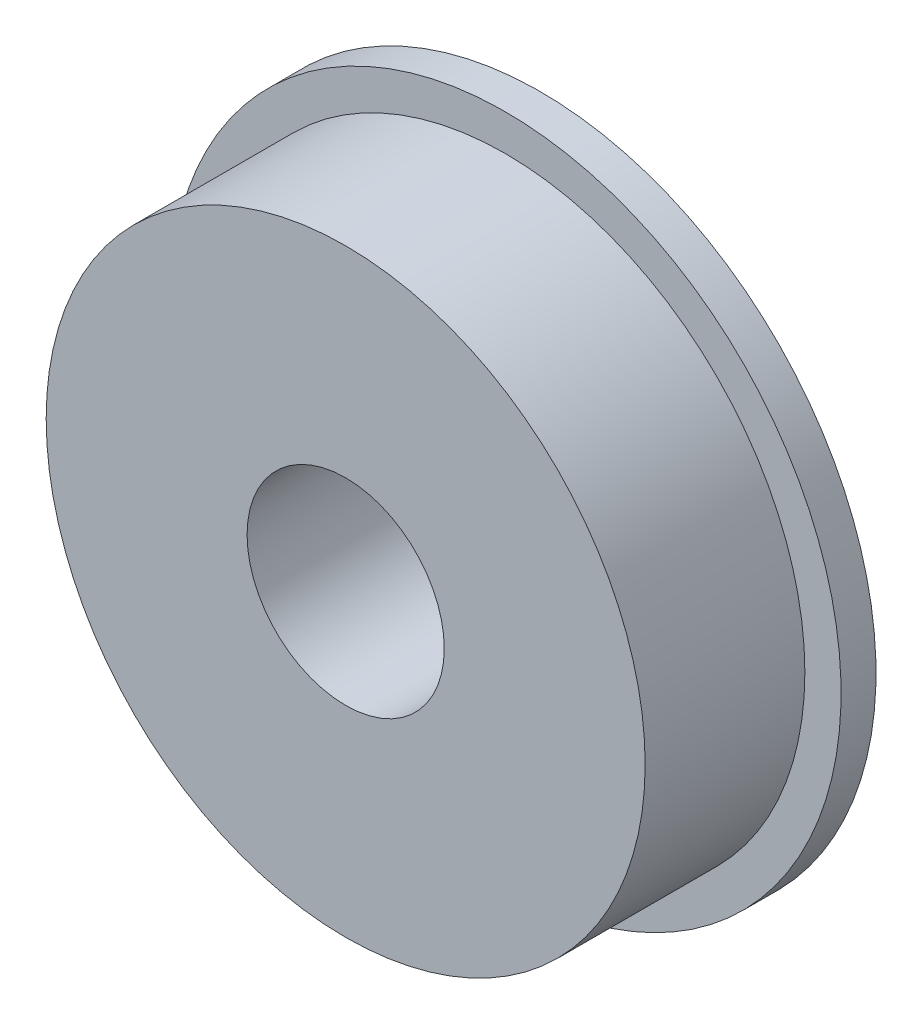
SolidWorks part; units mm, degrees
ref_plane "Front Plane" through (0, 0, 0) normal (0, 0, 1) x (1, 0, 0)
ref_plane "Top Plane" through (0, 0, 0) normal (0, 1, 0) x (1, 0, 0)
ref_plane "Right Plane" through (0, 0, 0) normal (1, 0, 0) x (0, 0, -1)
sketch "Sketch1" plane through (0, 0, 0) normal (0, 0, 1) x (1, 0, 0)
  circle A0 centre (0, 0) radius 12
  circle A1 centre (0, 0) radius 3.95
  dimension "D1" = 24
  dimension "D2" = 7.9
extrude "Boss-Extrude1" add sketch "Sketch1" along normal blind 6.4
sketch "Sketch2" plane through (0, 0, 0) normal (0, 0, -1) x (-1, 0, 0)
  circle A0 centre (0, 0) radius 13.45
  circle A1 centre (0, 0) radius 3.95
  dimension "D1" = 26.9
extrude "Boss-Extrude2" add sketch "Sketch2" along normal blind 1.4
